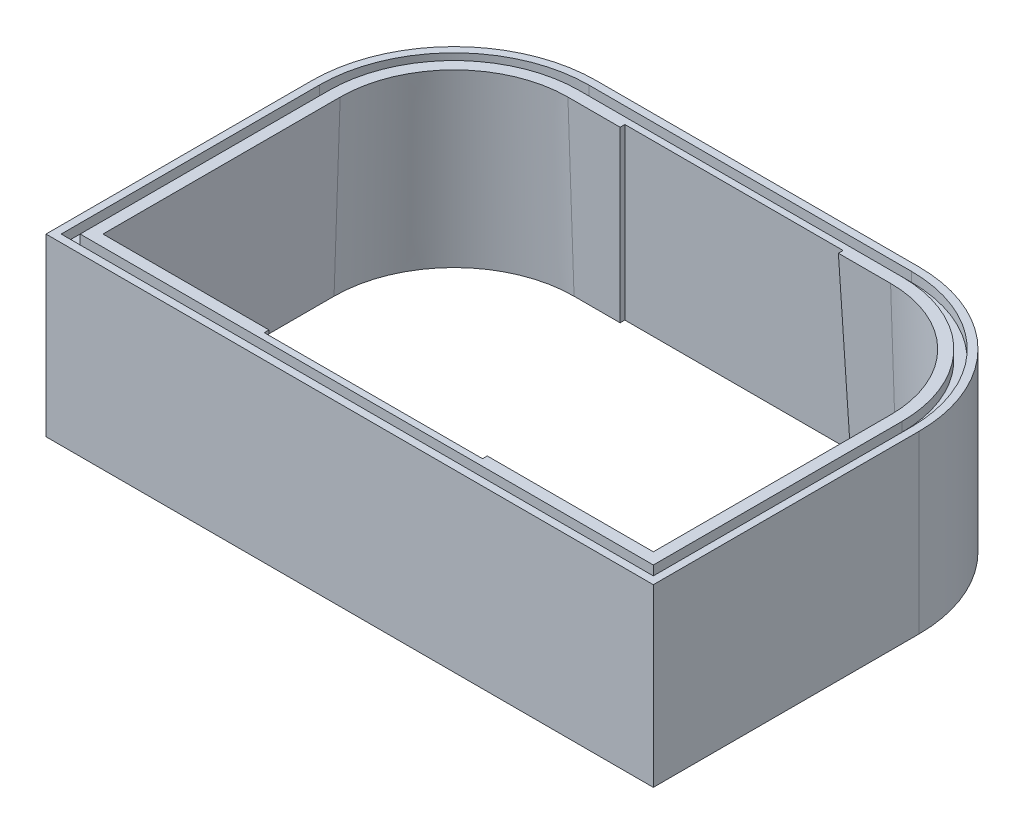
SolidWorks part; units mm, degrees
ref_plane "Ebene vorne" through (0, 0, 0) normal (0, 0, 1) x (1, 0, 0)
ref_plane "Ebene oben" through (0, 0, 0) normal (0, 1, 0) x (1, 0, 0)
ref_plane "Ebene rechts" through (0, 0, 0) normal (1, 0, 0) x (0, 0, -1)
sketch "Skizze1" plane through (0, 0, 0) normal (0, 1, 0) x (1, 0, 0)
  line L1 (0, 0) -> (640, 0)
  line L2 (0, 0) -> (0, 430)
  line L3 (0, 430) -> (640, 430)
  line L4 (640, 0) -> (640, 430)
  dimension "D1" = 640
  dimension "D2" = 430
extrude "Aufsatz-Linear austragen1" add sketch "Skizze1" along normal blind 185
fillet "Verrundung1" radius 150 2 edges at (0, 92.5, -430) (640, 92.5, -430)
sketch "Skizze2" plane through (0, 185, 0) normal (0, 1, 0) x (1, 0, 0)
  line L4 (490, 430) -> (150, 430) construction
  line L5 (0, 0) -> (640, 0) construction
  line L6 (640, 0) -> (640, 280) construction
  line L8 (490, 400) -> (150, 400)
  line L9 (30, 280) -> (30, 30)
  line L10 (30, 30) -> (610, 30)
  line L11 (610, 30) -> (610, 280)
  line L12 (490, 400) -> (435, 400)
  line L13 (30, 280) -> (30, 30)
  line L14 (30, 30) -> (205, 30)
  line L15 (610, 30) -> (610, 280)
  line L16 (205, 400) -> (150, 400)
  line L17 (205, 400) -> (205, 405)
  line L18 (435, 400) -> (435, 405)
  line L19 (205, 405) -> (435, 405)
  line L20 (435, 30) -> (610, 30)
  line L21 (435, 30) -> (435, 25)
  line L22 (205, 30) -> (205, 25)
  line L23 (435, 25) -> (205, 25)
  arc A4 (150, 400) -> (30, 280) centre (150, 280) ccw
  arc A5 (610, 280) -> (490, 400) centre (490, 280) ccw
  arc A6 (150, 400) -> (30, 280) centre (150, 280) ccw
  arc A7 (610, 280) -> (490, 400) centre (490, 280) ccw
  point P0 (212.2012, 133.5183)
  dimension "D2" = 25
  dimension "D3" = 25
  dimension "D4" = 205
  dimension "D1" = 30
extrude "Schnitt-Linear austragen1" cut sketch "Skizze2" against normal through all draft 2 draft outward yes
sketch "Skizze3" plane through (0, 185, 0) normal (0, 1, 0) x (1, 0, 0)
  line L8 (490, 422) -> (150, 422)
  line L9 (8, 280) -> (8, 8)
  line L10 (8, 8) -> (632, 8)
  line L11 (632, 8) -> (632, 280)
  line L12 (490, 422) -> (150, 422)
  line L13 (8, 280) -> (8, 8)
  line L14 (8, 8) -> (632, 8)
  line L15 (632, 8) -> (632, 280)
  arc A4 (150, 422) -> (8, 280) centre (150, 280) ccw
  arc A5 (632, 280) -> (490, 422) centre (490, 280) ccw
  arc A6 (150, 422) -> (8, 280) centre (150, 280) ccw
  arc A7 (632, 280) -> (490, 422) centre (490, 280) ccw
  dimension "D1" = 8
extrude "Schnitt-Linear-Austragen-Dünn1" cut sketch "Skizze3" against normal blind 10 thin thin type one direction reverse wall 10
